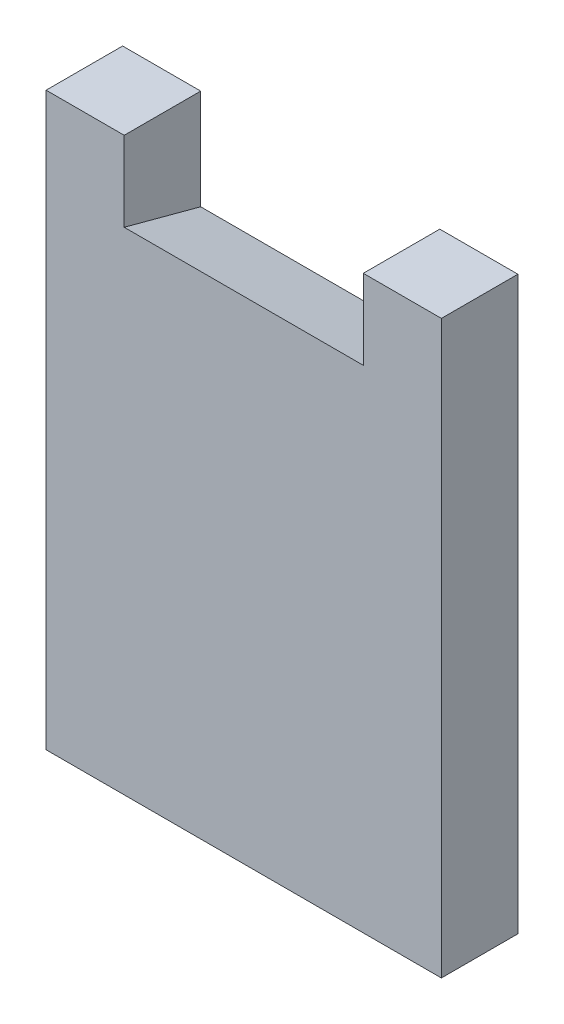
SolidWorks part; units mm, degrees
ref_plane "前视基准面" through (0, 0, 0) normal (0, 0, 1) x (1, 0, 0)
ref_plane "上视基准面" through (0, 0, 0) normal (0, 1, 0) x (1, 0, 0)
ref_plane "右视基准面" through (0, 0, 0) normal (1, 0, 0) x (0, 0, -1)
sketch "草图1" plane through (0, 0, 0) normal (0, 0, 1) x (1, 0, 0)
  line L1 (0, 0) -> (49.6, 0)
  line L2 (0, 0) -> (0, -71.68)
  line L3 (0, -71.68) -> (49.6, -71.68)
  line L4 (49.6, 0) -> (49.6, -71.68)
  line L5 (9.8, 0) -> (39.8, 0)
  line L6 (9.8, 0) -> (9.8, -10)
  line L7 (9.8, -10) -> (39.8, -10)
  line L8 (39.8, 0) -> (39.8, -10)
  point P9 (24.8, 0)
  dimension "D1" = 10
  dimension "D2" = 49.6
  dimension "D3" = 30
  dimension "D4" = 61.68
extrude "凸台-拉伸1" add sketch "草图1" along normal blind 9.6 contours L1 L8 L7 L6 L2 L3 L4
draft "拔模5" type of draft neutral plane draft angle 15 faces to draft 1 face at (24.8, -10, 4.8) neutral plane through (0, 0, 9.6) neutral plane normal (0, 0, 1) reverse direction yes parameters "D1"=15
